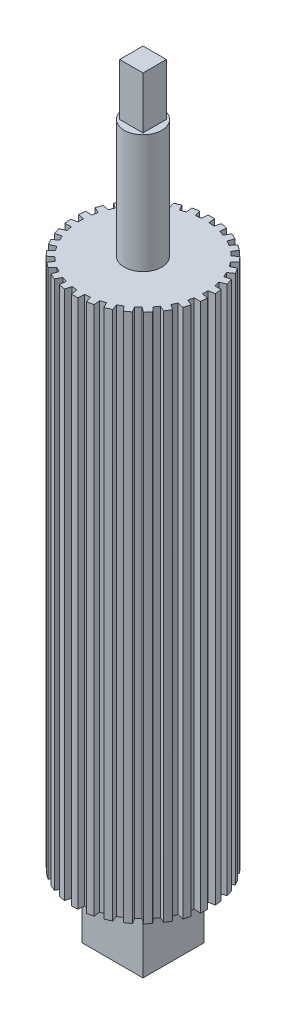
SolidWorks part; units mm, degrees
ref_plane "Front Plane" through (0, 0, 0) normal (0, 0, 1) x (1, 0, 0)
ref_plane "Top Plane" through (0, 0, 0) normal (0, 1, 0) x (1, 0, 0)
ref_plane "Right Plane" through (0, 0, 0) normal (1, 0, 0) x (0, 0, -1)
sketch "Sketch2" plane through (0, 0, 0) normal (0, 1, 0) x (1, 0, 0)
  line L1 (-0.7753, 12.6763) -> (-0.6703, 13.9539)
  line L2 (0.7753, 12.6763) -> (0.6703, 13.9539)
  line L3 (1.8772, 12.5605) -> (2.2456, 13.7883)
  line L4 (3.3939, 12.2381) -> (3.5568, 13.5096)
  line L5 (4.4476, 11.8957) -> (5.0633, 13.0201)
  line L6 (5.8642, 11.265) -> (6.2879, 12.4749)
  line L7 (6.8237, 10.7111) -> (7.6597, 11.6829)
  line L8 (8.0782, 9.7996) -> (8.7442, 10.895)
  line L9 (8.9015, 9.0583) -> (9.9213, 9.8351)
  line L10 (9.9391, 7.9059) -> (10.8183, 8.8389)
  line L11 (10.5903, 7.0096) -> (11.7493, 7.5574)
  line L12 (11.3657, 5.6667) -> (12.4196, 6.3965)
  line L13 (11.8163, 4.6546) -> (13.0638, 4.9494)
  line L14 (12.2955, 3.1798) -> (13.4781, 3.6745)
  line L15 (12.5258, 2.0961) -> (13.8074, 2.1252)
  line L16 (12.6879, 0.554) -> (13.9475, 0.792)
  line L17 (12.6879, -0.554) -> (13.9475, -0.792)
  line L18 (12.5258, -2.0961) -> (13.8074, -2.1252)
  line L19 (12.2955, -3.1798) -> (13.4781, -3.6745)
  line L20 (11.8163, -4.6546) -> (13.0638, -4.9494)
  line L21 (11.3657, -5.6667) -> (12.4196, -6.3965)
  line L22 (10.5903, -7.0096) -> (11.7493, -7.5574)
  line L23 (9.9391, -7.9059) -> (10.8183, -8.8389)
  line L24 (8.9015, -9.0583) -> (9.9213, -9.8351)
  line L25 (8.0782, -9.7996) -> (8.7442, -10.895)
  line L26 (6.8237, -10.7111) -> (7.6597, -11.6829)
  line L27 (5.8642, -11.265) -> (6.2879, -12.4749)
  line L28 (4.4476, -11.8957) -> (5.0633, -13.0201)
  line L29 (3.3939, -12.2381) -> (3.5568, -13.5096)
  line L30 (1.8772, -12.5605) -> (2.2456, -13.7883)
  line L31 (0.7753, -12.6763) -> (0.6703, -13.9539)
  line L32 (-0.7753, -12.6763) -> (-0.6703, -13.9539)
  line L33 (-1.8772, -12.5605) -> (-2.2456, -13.7883)
  line L34 (-3.3939, -12.2381) -> (-3.5568, -13.5096)
  line L35 (-4.4476, -11.8957) -> (-5.0633, -13.0201)
  line L36 (-5.8642, -11.265) -> (-6.2879, -12.4749)
  line L37 (-6.8237, -10.7111) -> (-7.6597, -11.6829)
  line L38 (-8.0782, -9.7996) -> (-8.7442, -10.895)
  line L39 (-8.9015, -9.0583) -> (-9.9213, -9.8351)
  line L40 (-9.9391, -7.9059) -> (-10.8183, -8.8389)
  line L41 (-10.5903, -7.0096) -> (-11.7493, -7.5574)
  line L42 (-11.3657, -5.6667) -> (-12.4196, -6.3965)
  line L43 (-11.8163, -4.6546) -> (-13.0638, -4.9494)
  line L44 (-12.2955, -3.1798) -> (-13.4781, -3.6745)
  line L45 (-12.5258, -2.0961) -> (-13.8074, -2.1252)
  line L46 (-12.6879, -0.554) -> (-13.9475, -0.792)
  line L47 (-12.6879, 0.554) -> (-13.9475, 0.792)
  line L48 (-12.5258, 2.0961) -> (-13.8074, 2.1252)
  line L49 (-12.2955, 3.1798) -> (-13.4781, 3.6745)
  line L50 (-11.8163, 4.6546) -> (-13.0638, 4.9494)
  line L51 (-11.3657, 5.6667) -> (-12.4196, 6.3965)
  line L52 (-10.5903, 7.0096) -> (-11.7493, 7.5574)
  line L53 (-9.9391, 7.9059) -> (-10.8183, 8.8389)
  line L54 (-8.9015, 9.0583) -> (-9.9213, 9.8351)
  line L55 (-8.0782, 9.7996) -> (-8.7442, 10.895)
  line L56 (-6.8237, 10.7111) -> (-7.6597, 11.6829)
  line L57 (-5.8642, 11.265) -> (-6.2879, 12.4749)
  line L58 (-4.4476, 11.8957) -> (-5.0633, 13.0201)
  line L59 (-3.3939, 12.2381) -> (-3.5568, 13.5096)
  line L60 (-1.8772, 12.5605) -> (-2.2456, 13.7883)
  arc A0 (-2.2456, 13.7883) -> (-3.5568, 13.5096) centre (0, 0) ccw
  arc A1 (-0.7753, 12.6763) -> (-1.8772, 12.5605) centre (0, 0) ccw
  arc A3 (-3.3939, 12.2381) -> (-4.4476, 11.8957) centre (0, 0) ccw
  arc A4 (-5.0633, 13.0201) -> (-6.2879, 12.4749) centre (0, 0) ccw
  arc A5 (-5.8642, 11.265) -> (-6.8237, 10.7111) centre (0, 0) ccw
  arc A6 (-7.6597, 11.6829) -> (-8.7442, 10.895) centre (0, 0) ccw
  arc A7 (-8.0782, 9.7996) -> (-8.9015, 9.0583) centre (0, 0) ccw
  arc A8 (-9.9213, 9.8351) -> (-10.8183, 8.8389) centre (0, 0) ccw
  arc A9 (-9.9391, 7.9059) -> (-10.5903, 7.0096) centre (0, 0) ccw
  arc A10 (-11.7493, 7.5574) -> (-12.4196, 6.3965) centre (0, 0) ccw
  arc A11 (-11.3657, 5.6667) -> (-11.8163, 4.6546) centre (0, 0) ccw
  arc A12 (-13.0638, 4.9494) -> (-13.4781, 3.6745) centre (0, 0) ccw
  arc A13 (-12.2955, 3.1798) -> (-12.5258, 2.0961) centre (0, 0) ccw
  arc A14 (-13.8074, 2.1252) -> (-13.9475, 0.792) centre (0, 0) ccw
  arc A15 (-12.6879, 0.554) -> (-12.6879, -0.554) centre (0, 0) ccw
  arc A16 (-13.9475, -0.792) -> (-13.8074, -2.1252) centre (0, 0) ccw
  arc A17 (-12.5258, -2.0961) -> (-12.2955, -3.1798) centre (0, 0) ccw
  arc A18 (-13.4781, -3.6745) -> (-13.0638, -4.9494) centre (0, 0) ccw
  arc A19 (-11.8163, -4.6546) -> (-11.3657, -5.6667) centre (0, 0) ccw
  arc A20 (-12.4196, -6.3965) -> (-11.7493, -7.5574) centre (0, 0) ccw
  arc A21 (-10.5903, -7.0096) -> (-9.9391, -7.9059) centre (0, 0) ccw
  arc A22 (-10.8183, -8.8389) -> (-9.9213, -9.8351) centre (0, 0) ccw
  arc A23 (-8.9015, -9.0583) -> (-8.0782, -9.7996) centre (0, 0) ccw
  arc A24 (-8.7442, -10.895) -> (-7.6597, -11.6829) centre (0, 0) ccw
  arc A25 (-6.8237, -10.7111) -> (-5.8642, -11.265) centre (0, 0) ccw
  arc A26 (-6.2879, -12.4749) -> (-5.0633, -13.0201) centre (0, 0) ccw
  arc A27 (-4.4476, -11.8957) -> (-3.3939, -12.2381) centre (0, 0) ccw
  arc A28 (-3.5568, -13.5096) -> (-2.2456, -13.7883) centre (0, 0) ccw
  arc A29 (-1.8772, -12.5605) -> (-0.7753, -12.6763) centre (0, 0) ccw
  arc A30 (-0.6703, -13.9539) -> (0.6703, -13.9539) centre (0, 0) ccw
  arc A31 (0.7753, -12.6763) -> (1.8772, -12.5605) centre (0, 0) ccw
  arc A32 (2.2456, -13.7883) -> (3.5568, -13.5096) centre (0, 0) ccw
  arc A33 (3.3939, -12.2381) -> (4.4476, -11.8957) centre (0, 0) ccw
  arc A34 (5.0633, -13.0201) -> (6.2879, -12.4749) centre (0, 0) ccw
  arc A35 (5.8642, -11.265) -> (6.8237, -10.7111) centre (0, 0) ccw
  arc A36 (7.6597, -11.6829) -> (8.7442, -10.895) centre (0, 0) ccw
  arc A37 (8.0782, -9.7996) -> (8.9015, -9.0583) centre (0, 0) ccw
  arc A38 (9.9213, -9.8351) -> (10.8183, -8.8389) centre (0, 0) ccw
  arc A39 (9.9391, -7.9059) -> (10.5903, -7.0096) centre (0, 0) ccw
  arc A40 (11.7493, -7.5574) -> (12.4196, -6.3965) centre (0, 0) ccw
  arc A41 (11.3657, -5.6667) -> (11.8163, -4.6546) centre (0, 0) ccw
  arc A42 (13.0638, -4.9494) -> (13.4781, -3.6745) centre (0, 0) ccw
  arc A43 (12.2955, -3.1798) -> (12.5258, -2.0961) centre (0, 0) ccw
  arc A44 (13.8074, -2.1252) -> (13.9475, -0.792) centre (0, 0) ccw
  arc A45 (12.6879, -0.554) -> (12.6879, 0.554) centre (0, 0) ccw
  arc A46 (13.9475, 0.792) -> (13.8074, 2.1252) centre (0, 0) ccw
  arc A47 (12.5258, 2.0961) -> (12.2955, 3.1798) centre (0, 0) ccw
  arc A48 (13.4781, 3.6745) -> (13.0638, 4.9494) centre (0, 0) ccw
  arc A49 (0.6703, 13.9539) -> (-0.6703, 13.9539) centre (0, 0) ccw
  arc A50 (3.5568, 13.5096) -> (2.2456, 13.7883) centre (0, 0) ccw
  arc A51 (6.2879, 12.4749) -> (5.0633, 13.0201) centre (0, 0) ccw
  arc A52 (8.7442, 10.895) -> (7.6597, 11.6829) centre (0, 0) ccw
  arc A53 (1.8772, 12.5605) -> (0.7753, 12.6763) centre (0, 0) ccw
  arc A54 (4.4476, 11.8957) -> (3.3939, 12.2381) centre (0, 0) ccw
  arc A55 (6.8237, 10.7111) -> (5.8642, 11.265) centre (0, 0) ccw
  arc A56 (8.9015, 9.0583) -> (8.0782, 9.7996) centre (0, 0) ccw
  arc A57 (10.5903, 7.0096) -> (9.9391, 7.9059) centre (0, 0) ccw
  arc A58 (10.8183, 8.8389) -> (9.9213, 9.8351) centre (0, 0) ccw
  arc A59 (12.4196, 6.3965) -> (11.7493, 7.5574) centre (0, 0) ccw
  arc A60 (11.8163, 4.6546) -> (11.3657, 5.6667) centre (0, 0) ccw
  point P129 (0, 0)
  dimension "D1" = 30
extrude "Boss-Extrude1" add sketch "Sketch2" along normal blind 211.1375 contours L39 A22 L40 A21 L41 A20 L42 A19 L43 A18 L44 A17 L45 A16 L46 A15 L47 A14 L48 A13 L49 A12 L50 A11 L51 A10 L52 A9 L53 A8 L54 A7 L55 A6 L56 A5 L57 A4 L58 A3 L59 A0 L60 A1 L1 A49 L2 A53 L3 A50 L4 A54 L5 A51 L6 A55 L7 A52 L8 A56 L9 A58 L10 A57 L11 A59 L12 A60 L13 A48 L14 A47 L15 A46 L16 A45 L17 A44 L18 A43 L19 A42 L20 A41 L21 A40 L22 A39 L23 A38 L24 A37 L25 A36 L26 A35 L27 A34 L28 A33 L29 A32 L30 A31 L31 A30 L32 A29 L33 A28 L34 A27 L35 A26 L36 A25 L37 A24 L38 A23
scale "Scale2" scale about centroid uniform scaling no x scale factor 0.96 y scale factor 1 z scale factor 0.96
sketch "Sketch3" plane through (0, 211.1375, 0) normal (0, 1, 0) x (1, 0, 0)
  circle A0 centre (0, 0) radius 3.6805
  dimension "D1" = 7.3609
extrude "Boss-Extrude2" add sketch "Sketch3" along normal blind 23.2093
sketch "Sketch4" plane through (0, 0, 0) normal (0, -1, 0) x (-1, 0, 0)
  circle A0 centre (0, 0) radius 3.6805
  dimension "D1" = 7.3609
extrude "Boss-Extrude3" add sketch "Sketch4" along normal blind 29.5593
sketch "Sketch6" plane through (0, 234.3467, 0) normal (0, 1, 0) x (1, 0, 0)
  line L1 (-2.286, -2.286) -> (2.286, -2.286)
  line L2 (-2.286, -2.286) -> (-2.286, 2.286)
  line L3 (-2.286, 2.286) -> (2.286, 2.286)
  line L4 (2.286, -2.286) -> (2.286, 2.286)
  line L9 (-2.286, -2.286) -> (2.286, 2.286) construction
  line L10 (-2.286, 2.286) -> (2.286, -2.286) construction
  point P0 (0, 0)
  dimension "D1" = 4.572
  dimension "D2" = 4.572
extrude "Boss-Extrude4" add sketch "Sketch6" along normal blind 10.16
sketch "Sketch7" plane through (0, -29.5593, 0) normal (0, -1, 0) x (1, 0, 0)
  circle A0 centre (0, 0) radius 17.3835
extrude "Cut-Extrude1" cut sketch "Sketch7" against normal blind 137.033 contours A0
sketch "Sketch8" plane through (0, 107.4737, 0) normal (0, -1, 0) x (1, 0, 0)
  line L1 (-5.969, 5.969) -> (5.969, 5.969)
  line L2 (-5.969, 5.969) -> (-5.969, -5.969)
  line L3 (-5.969, -5.969) -> (5.969, -5.969)
  line L4 (5.969, 5.969) -> (5.969, -5.969)
  line L5 (-5.969, 5.969) -> (5.969, -5.969) construction
  line L6 (-5.969, -5.969) -> (5.969, 5.969) construction
  point P0 (0, 0)
  dimension "D1" = 11.938
  dimension "D2" = 11.938
extrude "Boss-Extrude5" add sketch "Sketch8" along normal blind 12.7
